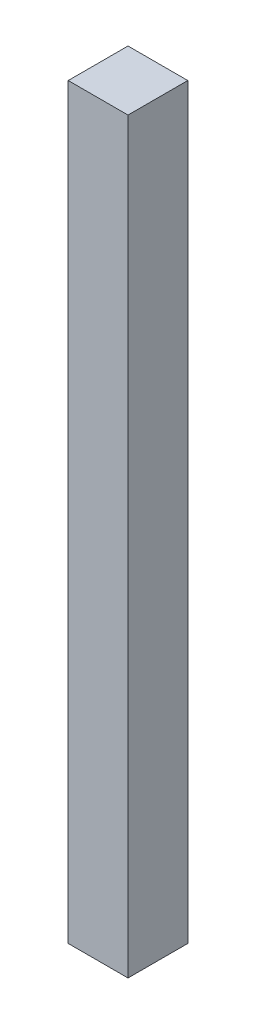
SolidWorks part; units mm, degrees
material "Stainless Steel (ferritic)"
ref_plane "Front Plane" through (0, 0, 0) normal (0, 0, 1) x (1, 0, 0)
ref_plane "Top Plane" through (0, 0, 0) normal (0, 1, 0) x (1, 0, 0)
ref_plane "Right Plane" through (0, 0, 0) normal (1, 0, 0) x (0, 0, -1)
sketch "Sketch1" plane through (0, 0, 0) normal (0, 0, 1) x (1, 0, 0)
  line L1 (-20, -250) -> (20, -250)
  line L2 (-20, -250) -> (-20, 250)
  line L3 (-20, 250) -> (20, 250)
  line L4 (20, -250) -> (20, 250)
  line L5 (-20, -250) -> (20, 250) construction
  line L6 (-20, 250) -> (20, -250) construction
  point P0 (0, 0)
  dimension "D1" = 40
  dimension "D2" = 500
extrude "Boss-Extrude1" add sketch "Sketch1" along normal blind 40
sketch "Sketch2" plane through (0, 0, 40) normal (0, 0, 1) x (1, 0, 0)
  line L0 (0, 250) -> (20, 250) construction
  line L1 (20, 250) -> (-20, 250) construction
  line L2 (10, 250) -> (10, -250) construction
  line L3 (-20, -250) -> (20, -250) construction
  line L4 (20, -250) -> (20, 250) construction
  point P8 (10, 200)
  point P9 (10, -200)
  point P10 (10, 100)
  point P11 (10, -100)
  point P12 (10, 0)
  dimension "D1" = 200
  dimension "D2" = 100
  dimension "D3" = 200
  dimension "D4" = 100
  dimension "D5" = 10
